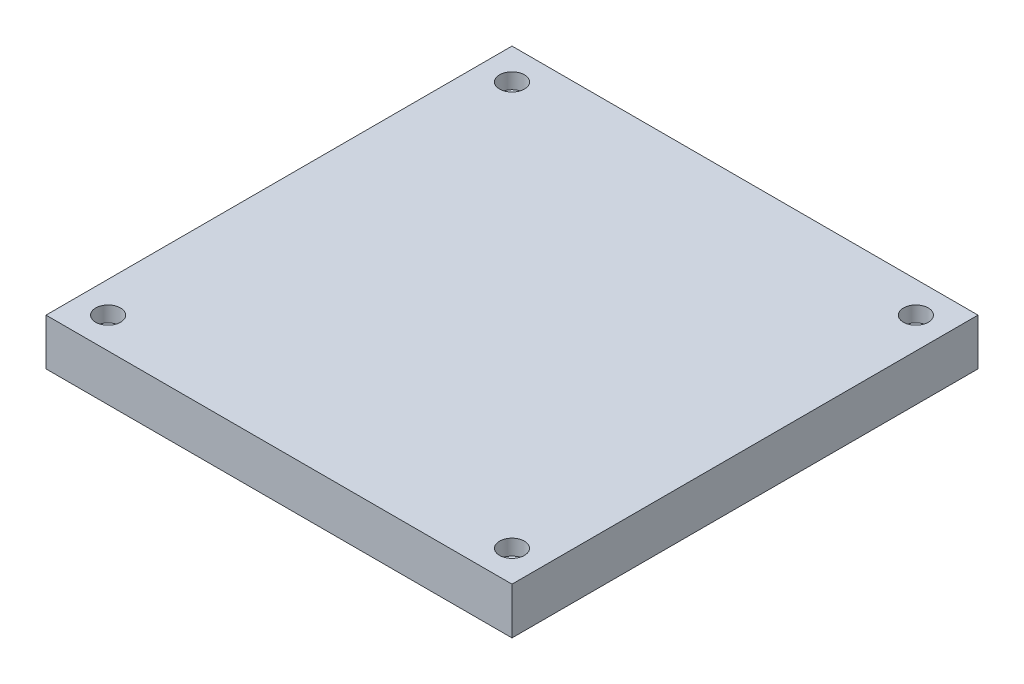
SolidWorks part; units mm, degrees
material "7075-T6 (SN)"
ref_plane "Plano frontal" through (0, 0, 0) normal (0, 0, 1) x (1, 0, 0)
ref_plane "Plano superior" through (0, 0, 0) normal (0, 1, 0) x (1, 0, 0)
ref_plane "Plano direito" through (0, 0, 0) normal (1, 0, 0) x (0, 0, -1)
sketch "Esboço1" plane through (0, 0, 0) normal (0, 1, 0) x (1, 0, 0)
  line L1 (-150, -150) -> (150, -150)
  line L2 (-150, -150) -> (-150, 150)
  line L3 (-150, 150) -> (150, 150)
  line L4 (150, -150) -> (150, 150)
  line L5 (-150, -150) -> (150, 150) construction
  line L6 (-150, 150) -> (150, -150) construction
  point P0 (0, 0)
  dimension "D1" = 300
extrude "Ressalto-extrusão1" add sketch "Esboço1" along normal blind 30
hole_wizard "Furo roscado de M14x2.01" [suppressed] positions "Esboço3" profile "Esboço2" tap size "M14x2.0" standard "Ansi Metric"
sketch "Esboço3" plane through (0, 0, 0) normal (0, -1, 0) x (-1, 0, 0)
  line L0 (0, 0) -> (0, -100) construction
  line L1 (100, -100) -> (-100, -100) construction
  line L2 (0, 0) -> (-100, 0) construction
  line L3 (-100, -100) -> (-100, 100) construction
  point P0 (47.5, -58)
  point P18 (-47.5, -58)
  point P21 (-47.5, 58)
  point P22 (47.5, 58)
  dimension "D1" = 95
  dimension "D2" = 116
sketch "Esboço2" plane through (-47.5, 0, 58) normal (1, 0, 0) x (0, 0, -1)
  line L0 (0, 0) -> (0, 13.6052)
  line L1 (0, 13.6052) -> (6, 10)
  line L2 (6, 10) -> (6, 0)
  line L5 (6, 0) -> (0, 0)
  line L10 (0, 13.6052) -> (-6, 10) construction
  line L11 (0, -6.35) -> (0, 107.95) construction
  dimension "Tap Drill Dia." = 12
  dimension "Tap Drill Depth" = 10
  dimension "Drill Angle" = 118
cosmetic thread "Rosca de furo1" [suppressed] parameters "D1"=10, "D2"=14
cosmetic thread "Rosca de furo2" [suppressed] parameters "D1"=10, "D2"=14
cosmetic thread "Rosca de furo3" [suppressed] parameters "D1"=10, "D2"=14
cosmetic thread "Rosca de furo4" [suppressed] parameters "D1"=10, "D2"=14
hole_wizard "Furo roscado de M10x1.51" [suppressed] positions "Esboço7" profile "Esboço6" tap size "M10x1.5" standard "Ansi Metric"
sketch "Esboço7" plane through (0, 20, 0) normal (0, 1, 0) x (1, 0, 0)
  line L0 (0, 0) -> (0, 100) construction
  line L1 (100, 100) -> (-100, 100) construction
  line L2 (0, 0) -> (100, 0) construction
  line L3 (100, -100) -> (100, 100) construction
  point P0 (-86.975, 86.975)
  point P13 (86.975, 86.975)
  point P14 (86.975, -86.975)
  point P15 (-86.975, -86.975)
  dimension "D1" = 173.95
  dimension "D2" = 173.95
sketch "Esboço6" plane through (-86.975, 20, -86.975) normal (1, 0, 0) x (0, 0, 1)
  line L0 (0, 0) -> (0, 12.5537)
  line L1 (0, 12.5537) -> (4.25, 10)
  line L2 (4.25, 10) -> (4.25, 0)
  line L5 (4.25, 0) -> (0, 0)
  line L10 (0, 12.5537) -> (-4.25, 10) construction
  line L11 (0, -6.35) -> (0, 107.95) construction
  dimension "Tap Drill Dia." = 8.5
  dimension "Tap Drill Depth" = 10
  dimension "Drill Angle" = 118
cosmetic thread "Rosca de furo5" [suppressed] parameters "D1"=10, "D2"=10
cosmetic thread "Rosca de furo6" [suppressed] parameters "D1"=10, "D2"=10
cosmetic thread "Rosca de furo7" [suppressed] parameters "D1"=10, "D2"=10
cosmetic thread "Rosca de furo8" [suppressed] parameters "D1"=10, "D2"=10
hole_wizard "Furo roscado de M16x2.01" positions "Esboço9" profile "Esboço8" tap size "M16x2.0" standard "Ansi Metric"
sketch "Esboço9" plane through (0, 0, 0) normal (0, -1, 0) x (-1, 0, 0)
  line L0 (0, 0) -> (0, -150) construction
  line L1 (150, -150) -> (-150, -150) construction
  line L2 (0, 0) -> (-150, 0) construction
  line L3 (-150, -150) -> (-150, 150) construction
  point P0 (55, -71)
  point P13 (-55, -71)
  point P15 (-55, 71)
  point P16 (55, 71)
  dimension "D1" = 110
  dimension "D2" = 142
sketch "Esboço8" plane through (-55, 0, 71) normal (1, 0, 0) x (0, 0, -1)
  line L0 (0, 0) -> (0, 14.206)
  line L1 (0, 14.206) -> (7, 10)
  line L2 (7, 10) -> (7, 0)
  line L5 (7, 0) -> (0, 0)
  line L10 (0, 14.206) -> (-7, 10) construction
  line L11 (0, -6.35) -> (0, 107.95) construction
  dimension "Tap Drill Dia." = 14
  dimension "Tap Drill Depth" = 10
  dimension "Drill Angle" = 118
cosmetic thread "Rosca de furo9" parameters "D1"=8, "D2"=16
cosmetic thread "Rosca de furo10" parameters "D1"=8, "D2"=16
cosmetic thread "Rosca de furo11" parameters "D1"=8, "D2"=16
cosmetic thread "Rosca de furo12" parameters "D1"=8, "D2"=16
hole_wizard "Furo roscado de M18x2.02" positions "Esboço11" profile "Esboço10" tap size "M18x2.0" standard "Ansi Metric"
sketch "Esboço11" plane through (0, 30, 0) normal (0, 1, 0) x (1, 0, 0)
  line L0 (0, 0) -> (0, 150) construction
  line L1 (150, 150) -> (-150, 150) construction
  line L2 (0, 0) -> (150, 0) construction
  line L3 (150, -150) -> (150, 150) construction
  point P0 (-130, 130)
  point P21 (130, 130)
  point P22 (130, -130)
  point P23 (-130, -130)
  dimension "D1" = 260
  dimension "D2" = 260
sketch "Esboço10" plane through (-130, 30, -130) normal (1, 0, 0) x (0, 0, 1)
  line L0 (0, 0) -> (0, 14.8069)
  line L1 (0, 14.8069) -> (8, 10)
  line L2 (8, 10) -> (8, 0)
  line L5 (8, 0) -> (0, 0)
  line L10 (0, 14.8069) -> (-8, 10) construction
  line L11 (0, -6.35) -> (0, 107.95) construction
  dimension "Tap Drill Dia." = 16
  dimension "Tap Drill Depth" = 10
  dimension "Drill Angle" = 118
cosmetic thread "Rosca de furo13" parameters "D1"=8, "D2"=18
cosmetic thread "Rosca de furo14" parameters "D1"=8, "D2"=18
cosmetic thread "Rosca de furo15" parameters "D1"=8, "D2"=18
cosmetic thread "Rosca de furo16" parameters "D1"=8, "D2"=18
equation "\"D2@Esboço7\"=\"D1@Esboço7\""
equation "\"D2@Esboço11\"=\"D1@Esboço11\""
